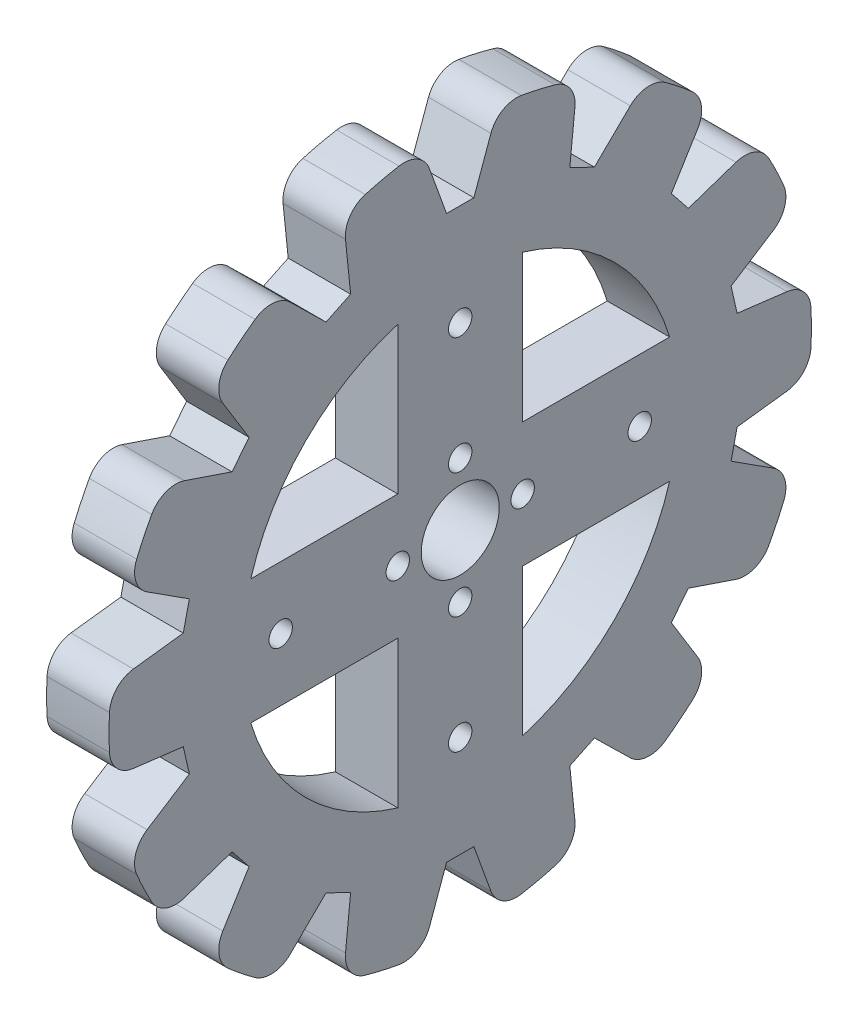
SolidWorks part; units mm, degrees
material "PMMA"
ref_plane "Front Plane" through (0, 0, 0) normal (0, 0, 1) x (1, 0, 0)
ref_plane "Top Plane" through (0, 0, 0) normal (0, 1, 0) x (1, 0, 0)
ref_plane "Right Plane" through (0, 0, 0) normal (1, 0, 0) x (0, 0, -1)
sketch "Sprocket" plane through (0, 0, 0) normal (1, 0, 0) x (0, 0, -1)
  circle A0 centre (0, 0) radius 45
  dimension "D1" = 90
extrude "Estrusione-Estrusione2" add sketch "Sprocket" along normal blind 8 contours A0
sketch "Tooth" plane through (0, 0, 0) normal (1, 0, 0) x (0, 0, -1)
  line L0 (-5, 45) -> (5, 45)
  line L1 (5, 45) -> (1.75, 36)
  line L2 (1.75, 36) -> (-1.75, 36)
  line L3 (-1.75, 36) -> (-5, 45)
  line L4 (-1.75, 36) -> (-1.75, 45) construction
  line L5 (1.75, 36) -> (1.75, 45) construction
  line L6 (-1.75, 36) -> (0, 31.1538) construction
  line L7 (0, 31.1538) -> (1.75, 36) construction
  line L8 (24.0296, 38.3742) -> (17.1965, 31.6756)
  line L9 (17.1965, 31.6756) -> (14.0431, 33.1942)
  line L10 (14.0431, 33.1942) -> (15.0199, 42.713)
  line L11 (15.0199, 42.713) -> (24.0296, 38.3742)
  line L12 (38.2999, 24.1479) -> (29.237, 21.0774)
  line L13 (29.237, 21.0774) -> (27.0548, 23.8138)
  line L14 (27.0548, 23.8138) -> (32.065, 31.9662)
  line L15 (32.065, 31.9662) -> (38.2999, 24.1479)
  line L16 (44.9844, 5.1388) -> (35.4868, 6.3046)
  line L17 (35.4868, 6.3046) -> (34.708, 9.7169)
  line L18 (34.708, 9.7169) -> (42.7592, 14.8881)
  line L19 (42.7592, 14.8881) -> (44.9844, 5.1388)
  line L20 (42.7592, -14.8881) -> (34.708, -9.7169)
  line L21 (34.708, -9.7169) -> (35.4868, -6.3046)
  line L22 (35.4868, -6.3046) -> (44.9844, -5.1388)
  line L23 (44.9844, -5.1388) -> (42.7592, -14.8881)
  line L24 (32.065, -31.9662) -> (27.0548, -23.8138)
  line L25 (27.0548, -23.8138) -> (29.237, -21.0774)
  line L26 (29.237, -21.0774) -> (38.2999, -24.1479)
  line L27 (38.2999, -24.1479) -> (32.065, -31.9662)
  line L28 (15.0199, -42.713) -> (14.0431, -33.1942)
  line L29 (14.0431, -33.1942) -> (17.1965, -31.6756)
  line L30 (17.1965, -31.6756) -> (24.0296, -38.3742)
  line L31 (24.0296, -38.3742) -> (15.0199, -42.713)
  line L32 (-5, -45) -> (-1.75, -36)
  line L33 (-1.75, -36) -> (1.75, -36)
  line L34 (1.75, -36) -> (5, -45)
  line L35 (5, -45) -> (-5, -45)
  line L36 (-24.0296, -38.3742) -> (-17.1965, -31.6756)
  line L37 (-17.1965, -31.6756) -> (-14.0431, -33.1942)
  line L38 (-14.0431, -33.1942) -> (-15.0199, -42.713)
  line L39 (-15.0199, -42.713) -> (-24.0296, -38.3742)
  line L40 (-38.2999, -24.1479) -> (-29.237, -21.0774)
  line L41 (-29.237, -21.0774) -> (-27.0548, -23.8138)
  line L42 (-27.0548, -23.8138) -> (-32.065, -31.9662)
  line L43 (-32.065, -31.9662) -> (-38.2999, -24.1479)
  line L44 (-44.9844, -5.1388) -> (-35.4868, -6.3046)
  line L45 (-35.4868, -6.3046) -> (-34.708, -9.7169)
  line L46 (-34.708, -9.7169) -> (-42.7592, -14.8881)
  line L47 (-42.7592, -14.8881) -> (-44.9844, -5.1388)
  line L48 (-42.7592, 14.8881) -> (-34.708, 9.7169)
  line L49 (-34.708, 9.7169) -> (-35.4868, 6.3046)
  line L50 (-35.4868, 6.3046) -> (-44.9844, 5.1388)
  line L51 (-44.9844, 5.1388) -> (-42.7592, 14.8881)
  line L52 (-32.065, 31.9662) -> (-27.0548, 23.8138)
  line L53 (-27.0548, 23.8138) -> (-29.237, 21.0774)
  line L54 (-29.237, 21.0774) -> (-38.2999, 24.1479)
  line L55 (-38.2999, 24.1479) -> (-32.065, 31.9662)
  line L56 (-15.0199, 42.713) -> (-14.0431, 33.1942)
  line L57 (-14.0431, 33.1942) -> (-17.1965, 31.6756)
  line L58 (-17.1965, 31.6756) -> (-24.0296, 38.3742)
  line L59 (-24.0296, 38.3742) -> (-15.0199, 42.713)
  line L60 (-28.1459, 22.4456) -> (-35.1824, 28.057) construction
  line L61 (-35.0974, 8.0108) -> (-43.8718, 10.0134) construction
  circle A0 centre (0, 0) radius 31.1538 construction
  circle A1 centre (0, 0) radius 45 construction
  point P67 (0, 0)
  dimension "D10" = 62.3077
  dimension "D1" = 10
  dimension "D2" = 3.5
  dimension "D3" = 9
  dimension "D4" = 70.145
  dimension "D5" = 70.145
  dimension "D6" = 3.25
  dimension "D7" = 3.25
  dimension "D8" = 39.71
  dimension "D9" = 13.8462
  dimension "D12" = 20.0269
  dimension "D11" = 14
extrude "Taglio-Estrusione1" cut sketch "Tooth" along normal through all
fillet "Raccordo1" radius 3.5 28 edges at (4, 38.1748, 23.8262) (4, 31.7235, 31.9158) (4, 24.0565, 38.0301) (4, 14.7341, 42.5195) (4, 5.1735, 44.7016) (4, -5.1735, 44.7016) (4, -14.7341, 42.5195) (4, -24.0565, 38.0301) (4, -31.7235, 31.9158) (4, -38.1748, 23.8262) (4, -42.4296, 14.9908) (4, -44.7321, 4.9032) (4, -44.7321, -4.9032) (4, -42.4296, -14.9908) (4, -38.1748, -23.8262) (4, -31.7235, -31.9158) (4, -24.0565, -38.0301) (4, -14.7341, -42.5195) (4, -5.1735, -44.7016) (4, 5.1735, -44.7016) (4, 14.7341, -42.5195) (4, 24.0565, -38.0301) (4, 31.7235, -31.9158) (4, 38.1748, -23.8262) (4, 42.4296, -14.9908) (4, 44.7321, -4.9032) (4, 44.7321, 4.9032) (4, 42.4296, 14.9908)
sketch "Schizzo1" plane through (0, 0, 0) normal (1, 0, 0) x (0, 0, -1)
  line L0 (0, 45) -> (0, -45) construction
  line L4 (-45, 0) -> (45, 0) construction
  circle A0 centre (0, 0) radius 5
  arc A1 (44.9453, -2.219) -> (44.9453, 2.219) centre (0, 0) ccw construction
  arc A2 (-44.9453, 2.219) -> (-44.9453, -2.219) centre (0, 0) ccw construction
  circle A3 centre (0, 8) radius 1.5
  circle A4 centre (8, 0) radius 1.5
  circle A5 centre (0, -8) radius 1.5
  circle A6 centre (-8, 0) radius 1.5
  arc A7 (-7.8379, 44.3122) -> (-12.1647, 43.3246) centre (0, 0) ccw construction
  arc A8 (7.8379, -44.3122) -> (12.1647, -43.3246) centre (0, 0) ccw construction
  circle A13 centre (0, 23) radius 1.5
  circle A14 centre (23, 0) radius 1.5
  circle A15 centre (0, -23) radius 1.5
  circle A16 centre (-23, 0) radius 1.5
  point P5 (0, 0)
  point P8 (0, 0)
  point P39 (0, 0)
  point P40 (0, 0)
  point P49 (0, 0)
  dimension "D1" = 10
  dimension "D2" = 3
  dimension "D9" = 15
  dimension "D10" = 3
  dimension "D3" = 8
  dimension "D4" = 4
  dimension "D11" = 4
extrude "Taglio-Estrusione2" cut sketch "Schizzo1" along direction (1, 0, 0) on the side of the normal through all
sketch "Schizzo2" plane through (8, 0, 0) normal (1, 0, 0) x (0, 0, -1)
  line L0 (-36, 0) -> (0, 0) construction
  line L1 (0, 36) -> (0, 0) construction
  line L2 (-29.237, 21.0774) -> (-27.0548, 23.8138) construction
  line L3 (-26.8328, 8) -> (-8, 8)
  line L4 (-8, 26.8328) -> (-8, 8)
  line L5 (26.8328, 8) -> (8, 8)
  line L6 (8, 26.8328) -> (8, 8)
  line L7 (8, -26.8328) -> (8, -8)
  line L8 (26.8328, -8) -> (8, -8)
  line L9 (-26.8328, -8) -> (-8, -8)
  line L10 (-8, -26.8328) -> (-8, -8)
  arc A0 (0, 36) -> (-36, 0) centre (0, 0) ccw construction
  arc A1 (-8, 26.8328) -> (-26.8328, 8) centre (0, 0) ccw
  arc A2 (26.8328, 8) -> (8, 26.8328) centre (0, 0) ccw
  arc A3 (8, -26.8328) -> (26.8328, -8) centre (0, 0) ccw
  arc A4 (-26.8328, -8) -> (-8, -26.8328) centre (0, 0) ccw
  point P22 (0, 0)
  dimension "D1" = 8
  dimension "D2" = 4
extrude "Taglio-Estrusione3" cut sketch "Schizzo2" against normal through all
sketch "Schizzo3" plane through (0, 0, 0) normal (1, 0, 0) x (0, 0, -1)
  line L0 (0, 4) -> (0, 5) construction
  line L1 (3.9686, -0.5) -> (4.9749, -0.5)
  line L2 (-0.5, 4.9749) -> (-0.5, 3.9686)
  line L3 (0.5, 3.9686) -> (0.5, 4.9749)
  line L4 (4.9749, 0.5) -> (3.9686, 0.5)
  line L5 (-0.5, -3.9686) -> (-0.5, -4.9749)
  line L6 (0.5, -4.9749) -> (0.5, -3.9686)
  line L7 (-3.9686, 0.5) -> (-4.9749, 0.5)
  line L8 (-4.9749, -0.5) -> (-3.9686, -0.5)
  circle A0 centre (0, 0) radius 2
  circle A1 centre (0, 0) radius 4
  circle A2 centre (0, 0) radius 5 construction
  arc A3 (-0.5, 4.9749) -> (0.5, 4.9749) centre (0, 0) cw
  arc A4 (-0.5, 3.9686) -> (0.5, 3.9686) centre (0, 0) cw
  arc A5 (4.9749, 0.5) -> (4.9749, -0.5) centre (0, 0) cw
  arc A6 (3.9686, 0.5) -> (3.9686, -0.5) centre (0, 0) cw
  arc A7 (0.5, -4.9749) -> (-0.5, -4.9749) centre (0, 0) cw
  arc A8 (0.5, -3.9686) -> (-0.5, -3.9686) centre (0, 0) cw
  arc A9 (-4.9749, -0.5) -> (-4.9749, 0.5) centre (0, 0) cw
  arc A10 (-3.9686, -0.5) -> (-3.9686, 0.5) centre (0, 0) cw
  point P30 (0, 0)
  dimension "D1" = 4
  dimension "D2" = 8
  dimension "D3" = 0.5
  dimension "D5" = 4
  dimension "D4" = 0.5
extrude "Estrusione-Estrusione3" [suppressed] add sketch "Schizzo3" along normal blind 8 separate body contours A1 A4 A0 | A4 L0 A3 L2 | L0 A1 L3 A3 | A9 L8 A1 L7 | A7 L6 A1 L5 | A5 L4 A1 L1
equation "\"Thickness8\"=8"
equation "\"D1@Estrusione-Estrusione2\"=\"Thickness8\""
equation "\"D\"=90"
equation "\"D1@Sprocket\"=\"D\""
equation "\"D10@Tooth\"=\"D\"-2*\"D9@Tooth\""
equation "\"D1@Estrusione-Estrusione3\"=\"Thickness8\""
